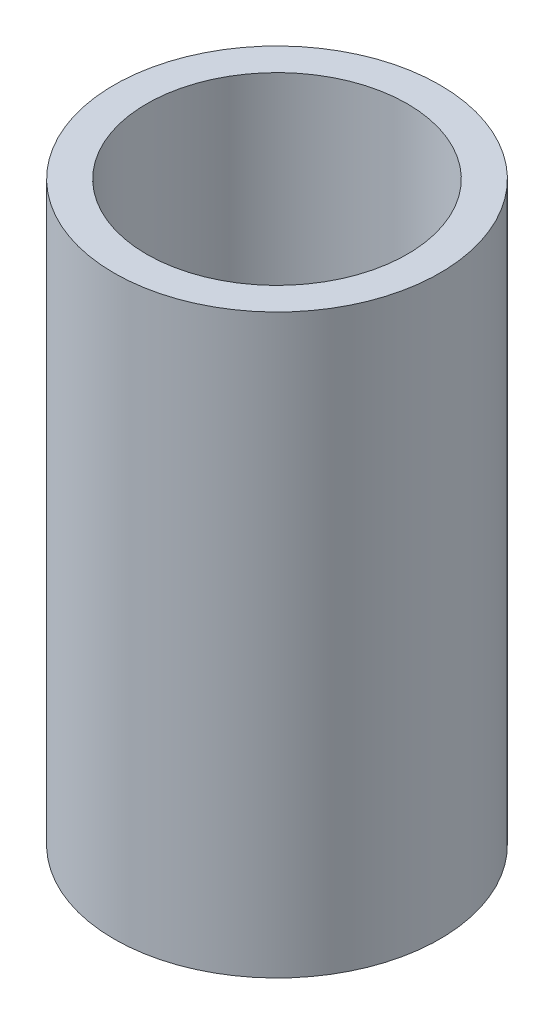
SolidWorks part; units mm, degrees
ref_plane "Front Plane" through (0, 0, 0) normal (0, 0, 1) x (1, 0, 0)
ref_plane "Top Plane" through (0, 0, 0) normal (0, 1, 0) x (1, 0, 0)
ref_plane "Right Plane" through (0, 0, 0) normal (1, 0, 0) x (0, 0, -1)
sketch "Sketch1" plane through (0, 0, 0) normal (0, 1, 0) x (1, 0, 0)
  circle A0 centre (0, 0) radius 5
  circle A1 centre (0, 0) radius 4
extrude "Boss-Extrude1" add sketch "Sketch1" along normal blind 17.7
